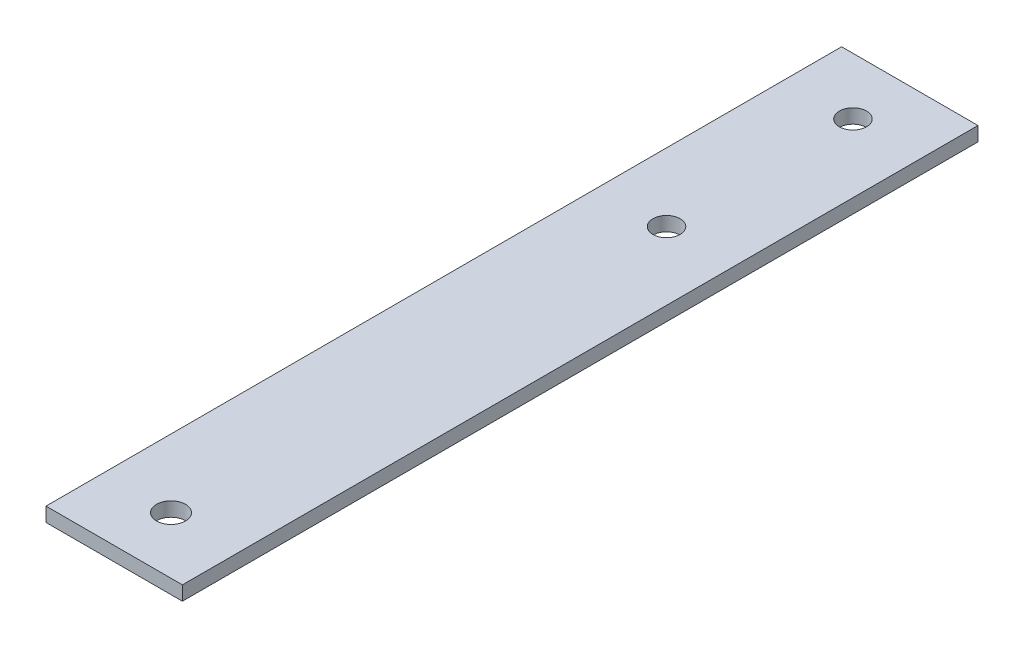
SolidWorks part; units mm, degrees
ref_plane "Front Plane" through (0, 0, 0) normal (0, 0, 1) x (1, 0, 0)
ref_plane "Top Plane" through (0, 0, 0) normal (0, 1, 0) x (1, 0, 0)
ref_plane "Right Plane" through (0, 0, 0) normal (1, 0, 0) x (0, 0, -1)
sketch "Sketch1" plane through (0, 0, 0) normal (0, 1, 0) x (1, 0, 0)
  line L0 (-20.7239, 88.9) -> (-20.7239, -88.9)
  line L1 (-51.2039, 88.9) -> (-20.7239, 88.9)
  line L2 (-51.2039, -88.9) -> (-20.7239, -88.9)
  line L3 (-51.2039, 88.9) -> (-51.2039, -88.9)
  circle A0 centre (-35.9639, 76.2) radius 3.048
  circle A1 centre (-35.9639, 34.5293) radius 3.048
  circle A2 centre (-35.9639, -76.2) radius 3.2385
  point P1 (-35.9639, 88.9)
  dimension "D1" = 6.096
  dimension "D4" = 6.477
  dimension "D2" = 12.7
  dimension "D3" = 41.6707
extrude "Boss-Extrude1" add sketch "Sketch1" along normal blind 3.175
